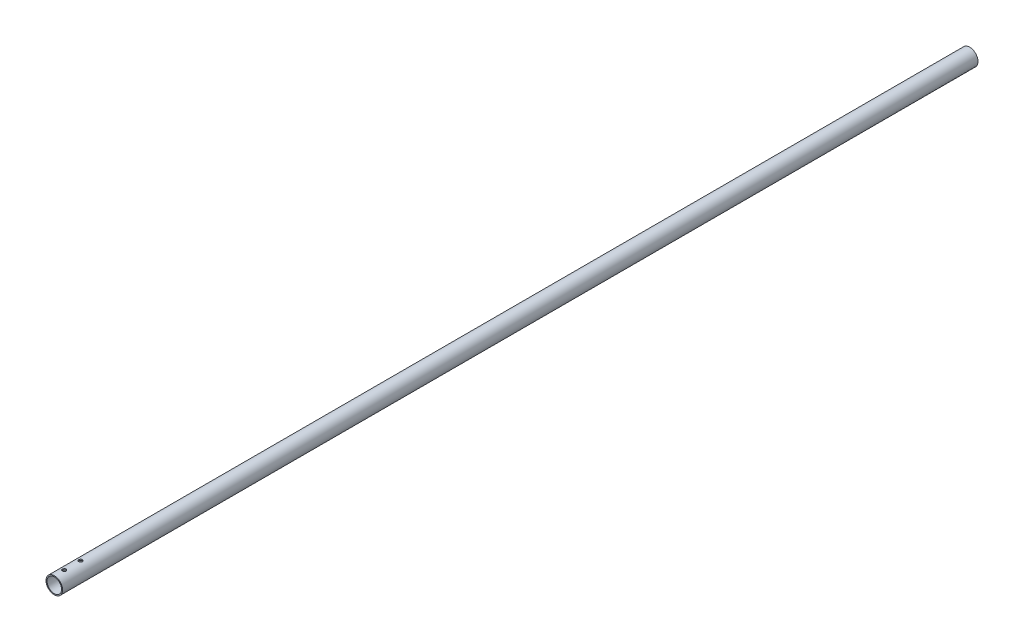
SolidWorks part; units mm, degrees
material "1060 Alloy"
ref_plane "Front Plane" through (0, 0, 0) normal (0, 0, 1) x (1, 0, 0)
ref_plane "Top Plane" through (0, 0, 0) normal (0, 1, 0) x (1, 0, 0)
ref_plane "Right Plane" through (0, 0, 0) normal (1, 0, 0) x (0, 0, -1)
sketch "Sketch2" plane through (0, 0, 0) normal (0, 0, 1) x (1, 0, 0)
  circle A0 centre (0, 0) radius 12.7
  circle A1 centre (0, 0) radius 11.1125
  dimension "D1" = 25.4
  dimension "D2" = 22.225
extrude "Boss-Extrude1" add sketch "Sketch2" along normal blind 1400
sketch "Sketch3" plane through (0, 0, 0) normal (0, 1, 0) x (1, 0, 0)
  line L0 (0, -1400) -> (0, -1392.75) construction
  line L1 (-12.7, -1400) -> (12.7, -1400) construction
  line L2 (0, -1392.75) -> (0, -1372.75) construction
  dimension "D1" = 7.25
  dimension "D2" = 20
hole_wizard "M5 Clearance Hole1" positions "Sketch4" profile "Sketch6" hole size "M5" standard "AS"
sketch "Sketch4" plane through (0, 0, 0) normal (0, 1, 0) x (1, 0, 0)
  line L0 (-12.7, -1400) -> (12.7, -1400) construction
  point P0 (0, -1385)
  point P6 (0, -1360)
  dimension "D1" = 25
  dimension "D2" = 15
sketch "Sketch6" plane through (0, 0, 1385) normal (1, 0, 0) x (0, 0, -1)
  line L0 (0, 0) -> (0, 12.7)
  line L1 (0, 12.7) -> (2.75, 12.7)
  line L2 (2.75, 12.7) -> (2.75, 0)
  line L5 (2.75, 0) -> (0, 0)
  line L11 (0, -6.35) -> (0, 107.95) construction
  dimension "Thru Hole Dia." = 5.5
  dimension "Thru Hole Depth" = 12.7
mirror "Mirror1" about plane through (0, 0, 0) normal (0, 1, 0) of "M5 Clearance Hole1"
equation "\"keelOutDiameter\"= 1in"
equation "\"keelInDiameter\"= \"keelOutDiameter\" - 0.125in"
equation "\"D1@Sketch2\"=\"keelOutDiameter\""
equation "\"D2@Sketch2\"=\"keelInDiameter\""
equation "\"frontBoltClearance\"= 7.25mm"
equation "\"D1@Sketch3\"=\"frontBoltClearance\""
equation "\"betweenBoltsDistance\"= 20mm"
equation "\"D2@Sketch3\"=\"betweenBoltsDistance\""
equation "\"wingLength\"= 1.4m"
equation "\"D1@Boss-Extrude1\"=\"wingLength\""
